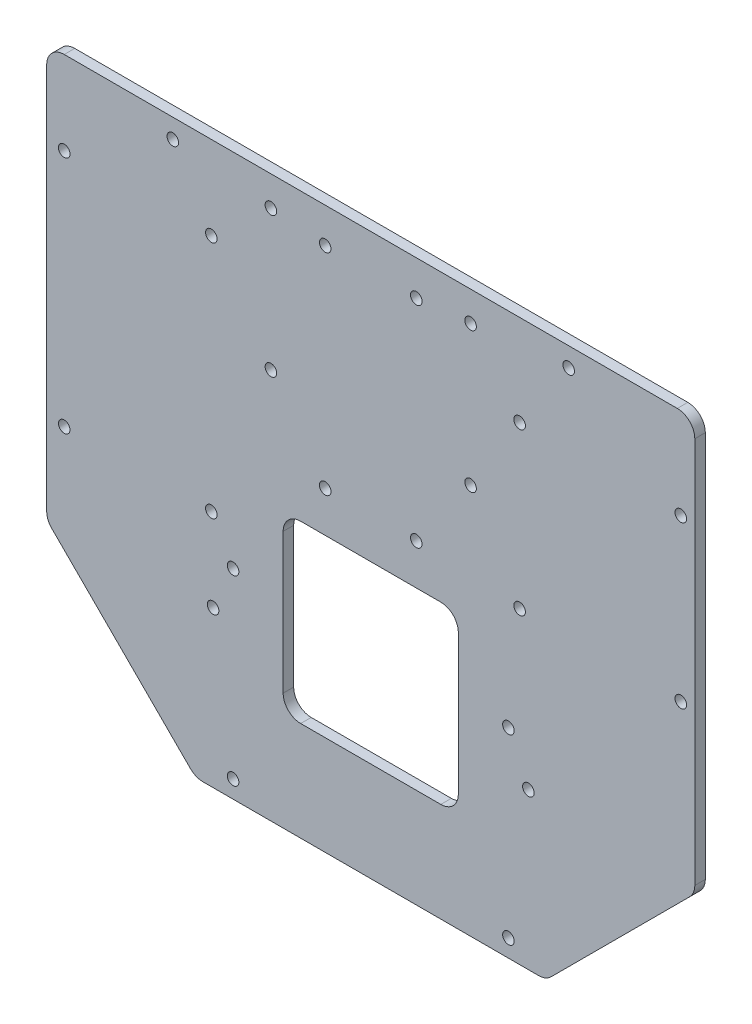
SolidWorks part; units mm, degrees
ref_plane "前视基准面" through (0, 0, 0) normal (0, 0, 1) x (1, 0, 0)
ref_plane "上视基准面" through (0, 0, 0) normal (0, 1, 0) x (1, 0, 0)
ref_plane "右视基准面" through (0, 0, 0) normal (1, 0, 0) x (0, 0, -1)
sketch "草图1" plane through (0, 0, 0) normal (0, 0, 1) x (1, 0, 0)
  line L1 (-87.5, 103.8596) -> (87.5, 103.8596)
  line L2 (-92.5, 98.8596) -> (-92.5, -13.6404)
  line L3 (-50, -56.1404) -> (50, -56.1404)
  line L4 (92.5, 98.8596) -> (92.5, -13.6404)
  line L5 (-92.5, 103.8596) -> (50, -56.1404) construction
  line L6 (-50, -56.1404) -> (92.5, 103.8596) construction
  line L7 (0, 103.8596) -> (0, -56.1404) construction
  line L9 (-92.5, -13.6404) -> (-50, -56.1404)
  line L10 (92.5, -13.6404) -> (50, -56.1404)
  arc A0 (87.5, 103.8596) -> (92.5, 98.8596) centre (87.5, 98.8596) cw
  arc A1 (-87.5, 103.8596) -> (-92.5, 98.8596) centre (-87.5, 98.8596) ccw
  point P0 (0, 0)
  dimension "D5" = 5
  dimension "D1" = 185
  dimension "D2" = 160
  dimension "D3" = 135
  dimension "D4" = 100
extrude "凸台-拉伸1" add sketch "草图1" along normal blind 3
sketch "草图2" plane through (0, 0, 3) normal (0, 0, 1) x (1, 0, 0)
  line L0 (87.5, 103.8596) -> (-87.5, 103.8596) construction
  line L1 (-28.5, 95.3596) -> (28.5, 95.3596) construction
  line L2 (-28.5, 95.3596) -> (-28.5, 55.3596) construction
  line L3 (-28.5, 55.3596) -> (28.5, 55.3596) construction
  line L4 (28.5, 95.3596) -> (28.5, 55.3596) construction
  line L5 (-28.5, 95.3596) -> (28.5, 55.3596) construction
  line L6 (-28.5, 55.3596) -> (28.5, 95.3596) construction
  line L7 (0, 0) -> (0, 75.3596) construction
  circle A0 centre (-28.5, 95.3596) radius 1.65
  circle A1 centre (28.5, 95.3596) radius 1.65
  circle A2 centre (-28.5, 55.3596) radius 1.65
  circle A3 centre (28.5, 55.3596) radius 1.65
  point P0 (0, 75.3596)
  dimension "D4" = 3.3
  dimension "D1" = 28.5
  dimension "D2" = 57
  dimension "D3" = 40
extrude "切除-拉伸1" cut sketch "草图2" against normal blind 10
sketch "草图3" plane through (0, 0, 3) normal (0, 0, 1) x (1, 0, 0)
  line L0 (-92.5, 98.8596) -> (-92.5, -13.6404) construction
  line L1 (-87.5, 80.0596) -> (-45.5, 80.0596) construction
  line L2 (-87.5, 80.0596) -> (-87.5, 11.8596) construction
  line L3 (-87.5, 11.8596) -> (-45.5, 11.8596) construction
  line L4 (-45.5, 80.0596) -> (-45.5, 11.8596) construction
  line L5 (-50, -56.1404) -> (50, -56.1404) construction
  circle A0 centre (-87.5, 80.0596) radius 1.65
  circle A1 centre (-45.5, 80.0596) radius 1.65
  circle A2 centre (-87.5, 11.8596) radius 1.65
  circle A3 centre (-45.5, 11.8596) radius 1.65
  dimension "D5" = 3.3
  dimension "D1" = 68.2
  dimension "D2" = 42
  dimension "D3" = 5
  dimension "D4" = 68
extrude "切除-拉伸2" cut sketch "草图3" against normal blind 10
sketch "草图4" plane through (0, 0, 3) normal (0, 0, 1) x (1, 0, 0)
  line L0 (92.5, -13.6404) -> (92.5, 98.8596) construction
  line L1 (42.5, 77.8596) -> (88.5, 77.8596) construction
  line L2 (42.5, 77.8596) -> (42.5, 31.8596) construction
  line L3 (42.5, 31.8596) -> (88.5, 31.8596) construction
  line L4 (88.5, 77.8596) -> (88.5, 31.8596) construction
  line L5 (87.5, 103.8596) -> (-87.5, 103.8596) construction
  circle A0 centre (42.5, 77.8596) radius 1.65
  circle A1 centre (88.5, 77.8596) radius 1.65
  circle A2 centre (42.5, 31.8596) radius 1.65
  circle A3 centre (88.5, 31.8596) radius 1.65
  dimension "D5" = 3.3
  dimension "D1" = 46
  dimension "D2" = 46
  dimension "D3" = 4
  dimension "D4" = 26
extrude "切除-拉伸3" cut sketch "草图4" against normal blind 10
sketch "草图5" plane through (0, 0, 3) normal (0, 0, 1) x (1, 0, 0)
  line L0 (-50, -56.1404) -> (50, -56.1404) construction
  line L1 (-39.3, 0.8596) -> (39.3, 0.8596) construction
  line L2 (-39.3, 0.8596) -> (-39.3, -51.1404) construction
  line L3 (-39.3, -51.1404) -> (39.3, -51.1404) construction
  line L4 (39.3, 0.8596) -> (39.3, -51.1404) construction
  line L5 (0, -56.1404) -> (0, 103.8596) construction
  line L6 (87.5, 103.8596) -> (-87.5, 103.8596) construction
  circle A0 centre (-39.3, 0.8596) radius 1.65
  circle A1 centre (39.3, 0.8596) radius 1.65
  circle A2 centre (-39.3, -51.1404) radius 1.65
  circle A3 centre (39.3, -51.1404) radius 1.65
  dimension "D4" = 3.3
  dimension "D1" = 78.6
  dimension "D2" = 52
  dimension "D3" = 5
extrude "切除-拉伸4" cut sketch "草图5" against normal blind 10
sketch "草图6" plane through (0, 0, 3) normal (0, 0, 1) x (1, 0, 0)
  line L0 (87.5, 103.8596) -> (-87.5, 103.8596) construction
  line L1 (-56.5, 98.3596) -> (56.5, 98.3596) construction
  line L2 (-56.5, 98.3596) -> (-56.5, -11.6404) construction
  line L3 (-56.5, -11.6404) -> (56.5, -11.6404) construction
  line L4 (56.5, 98.3596) -> (56.5, -11.6404) construction
  line L7 (0, -56.1404) -> (0, 98.3596) construction
  line L8 (-50, -56.1404) -> (50, -56.1404) construction
  circle A0 centre (-56.5, 98.3596) radius 1.65
  circle A1 centre (56.5, 98.3596) radius 1.65
  circle A4 centre (-45, -11.6404) radius 1.65
  circle A5 centre (45, -11.6404) radius 1.65
  dimension "D5" = 3.3
  dimension "D7" = 3.3
  dimension "D1" = 5.5
  dimension "D2" = 113
  dimension "D3" = 110
  dimension "D6" = 90
extrude "切除-拉伸5" cut sketch "草图6" against normal blind 10
sketch "草图7" plane through (0, 0, 3) normal (0, 0, 1) x (1, 0, 0)
  line L0 (0, 0) -> (0, 63.8596) construction
  line L1 (-13, 33.8596) -> (13, 33.8596) construction
  line L2 (-13, 33.8596) -> (-13, 93.8596) construction
  line L3 (-13, 93.8596) -> (13, 93.8596) construction
  line L4 (13, 33.8596) -> (13, 93.8596) construction
  line L5 (-13, 33.8596) -> (13, 93.8596) construction
  line L6 (-13, 93.8596) -> (13, 33.8596) construction
  line L8 (87.5, 103.8596) -> (-87.5, 103.8596) construction
  circle A0 centre (-13, 93.8596) radius 1.65
  circle A1 centre (13, 93.8596) radius 1.65
  circle A2 centre (13, 33.8596) radius 1.65
  circle A3 centre (-13, 33.8596) radius 1.65
  point P0 (0, 63.8596)
  dimension "D1" = 3.3
  dimension "D2" = 26
  dimension "D3" = 60
  dimension "D4" = 10
extrude "切除-拉伸6" cut sketch "草图7" against normal blind 10
sketch "草图8" plane through (0, 0, 3) normal (0, 0, 1) x (1, 0, 0)
  line L0 (0, 0) -> (0, 71.5605) construction
  line L2 (-20, 22.2174) -> (20, 22.2174)
  line L3 (-25, 17.2174) -> (-25, -22.7826)
  line L4 (-20, -27.7826) -> (20, -27.7826)
  line L5 (25, 17.2174) -> (25, -22.7826)
  line L6 (-25, 22.2174) -> (25, -27.7826) construction
  line L7 (-25, -27.7826) -> (25, 22.2174) construction
  arc A0 (20, 22.2174) -> (25, 17.2174) centre (20, 17.2174) cw
  arc A1 (20, -27.7826) -> (25, -22.7826) centre (20, -22.7826) ccw
  arc A2 (-25, -22.7826) -> (-20, -27.7826) centre (-20, -22.7826) ccw
  arc A3 (-20, 22.2174) -> (-25, 17.2174) centre (-20, 17.2174) ccw
  point P3 (0, -2.7826)
  dimension "D1" = 5
  dimension "D2" = 50
  dimension "D3" = 50
extrude "切除-拉伸7" cut sketch "草图8" against normal blind 10
fillet "圆角1" radius 5 4 edges at (92.5, -13.6404, 1.5) (50, -56.1404, 1.5) (-50, -56.1404, 1.5) (-92.5, -13.6404, 1.5)
